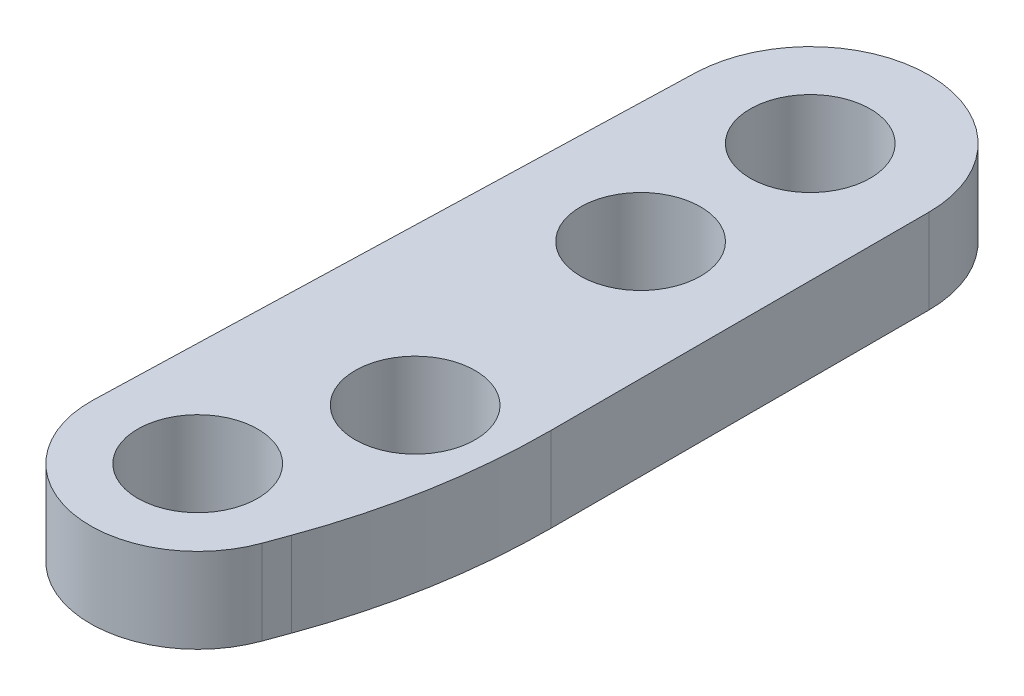
SolidWorks part; units mm, degrees
material "6061-T6 (SS)"
ref_plane "Front Plane" through (0, 0, 0) normal (0, 0, 1) x (1, 0, 0)
ref_plane "Top Plane" through (0, 0, 0) normal (0, 1, 0) x (1, 0, 0)
ref_plane "Right Plane" through (0, 0, 0) normal (1, 0, 0) x (0, 0, -1)
sketch "Sketch7" plane through (0, 0, 0) normal (0, 1, 0) x (1, 0, 0)
  line L0 (0, 0) -> (2.1718, 5.967) construction
  line L1 (0, 0) -> (2.1718, 0) construction
  line L2 (0, 0) -> (1.7901, -0.6515) construction
  line L3 (1.7901, -0.6515) -> (3.7791, -1.3755) construction
  line L8 (5.5309, 21.842) -> (5.5309, 7.689)
  line L10 (-4.0198, 0.1219) -> (-3.357, 21.9768)
  line L12 (1.0859, 21.842) -> (1.0859, 2.9835) construction
  line L13 (1.0859, 2.9835) -> (-3.933, 2.9835) construction
  line L14 (1.0859, 2.9835) -> (2.1718, 0) construction
  line L15 (0, 2.9835) -> (1.0859, 5.967) construction
  line L16 (1.0859, 21.842) -> (-24.3141, 21.842) construction
  line L17 (-24.3141, 15.492) -> (-24.3141, 21.842) construction
  line L18 (-24.3141, 15.492) -> (-24.3141, 5.967) construction
  line L19 (-24.3141, 15.492) -> (1.0859, 15.492) construction
  line L22 (-24.3141, 5.967) -> (1.0859, 5.967) construction
  line L23 (1.0859, 21.842) -> (2.9909, 21.842) construction
  line L24 (2.9909, 21.842) -> (5.5309, 21.842) construction
  line L25 (3.7791, -1.3755) -> (4.0768, -0.5576)
  circle A0 centre (0, 0) radius 1.905 construction
  circle A1 centre (2.1718, 5.967) radius 1.905 construction
  arc A12 (-4.0198, 0.1219) -> (3.7791, -1.3755) centre (0, 0) ccw
  arc A14 (-3.357, 21.9768) -> (5.5309, 21.842) centre (1.0859, 21.842) cw
  circle A15 centre (1.0859, 21.842) radius 1.905 construction
  circle A17 centre (1.0859, 15.492) radius 1.905 construction
  arc A20 (4.0768, -0.5576) -> (5.5309, 7.689) centre (-18.5803, 7.689) ccw
  point P9 (0, 0)
  point P14 (1.0859, 2.9835)
  point P23 (0, 0)
  point P27 (0, 0)
  point P28 (6.8009, 14.574)
  point P31 (0, 0)
  point P32 (0, 0)
  point P34 (4.0768, -0.6515)
  point P35 (-24.3141, 6.3547)
  point P37 (4.0768, 5.967)
  dimension "D1" = 3.81
  dimension "D5" = 3.81
  dimension "D6" = 6.35
  dimension "D2" = 6.35
  dimension "D3" = 70
  dimension "D4" = 2.1167
  dimension "D7" = 25.4
  dimension "D8" = 2.54
  dimension "D9" = 90
  dimension "D10" = 9.525
extrude "Boss-Extrude3" add sketch "Sketch7" along normal blind 3.175
hole_wizard "#8 Clearance Hole1" positions "Sketch8" profile "Sketch9" hole size "#8" standard "ANSI Inch"
sketch "Sketch8" plane through (0, 3.175, 0) normal (0, 1, 0) x (1, 0, 0)
  point P0 (2.1718, 5.967)
  point P3 (0, 0)
sketch "Sketch9" plane through (2.1718, 3.175, -5.967) normal (1, 0, 0) x (0, 0, 1)
  line L0 (0, 0) -> (0, 42.7527)
  line L1 (0, 42.7527) -> (2.2479, 41.402)
  line L2 (2.2479, 41.402) -> (2.2479, 0)
  line L5 (2.2479, 0) -> (0, 0)
  line L10 (0, 42.7527) -> (-2.2479, 41.402) construction
  line L11 (0, -6.35) -> (0, 107.95) construction
  dimension "Hole Dia." = 4.4958
  dimension "Hole Depth" = 41.402
  dimension "Drill Angle" = 118
hole_wizard "#8 Clearance Hole2" positions "Sketch10" profile "Sketch11" hole size "#8" standard "ANSI Inch"
sketch "Sketch10" plane through (0, 3.175, 0) normal (0, 1, 0) x (1, 0, 0)
  point P0 (1.0859, 21.842)
  point P3 (1.0859, 15.492)
sketch "Sketch11" plane through (1.0859, 3.175, -21.842) normal (1, 0, 0) x (0, 0, 1)
  line L0 (0, 0) -> (0, 42.7527)
  line L1 (0, 42.7527) -> (2.2479, 41.402)
  line L2 (2.2479, 41.402) -> (2.2479, 0)
  line L5 (2.2479, 0) -> (0, 0)
  line L10 (0, 42.7527) -> (-2.2479, 41.402) construction
  line L11 (0, -6.35) -> (0, 107.95) construction
  dimension "Hole Dia." = 4.4958
  dimension "Hole Depth" = 41.402
  dimension "Drill Angle" = 118
